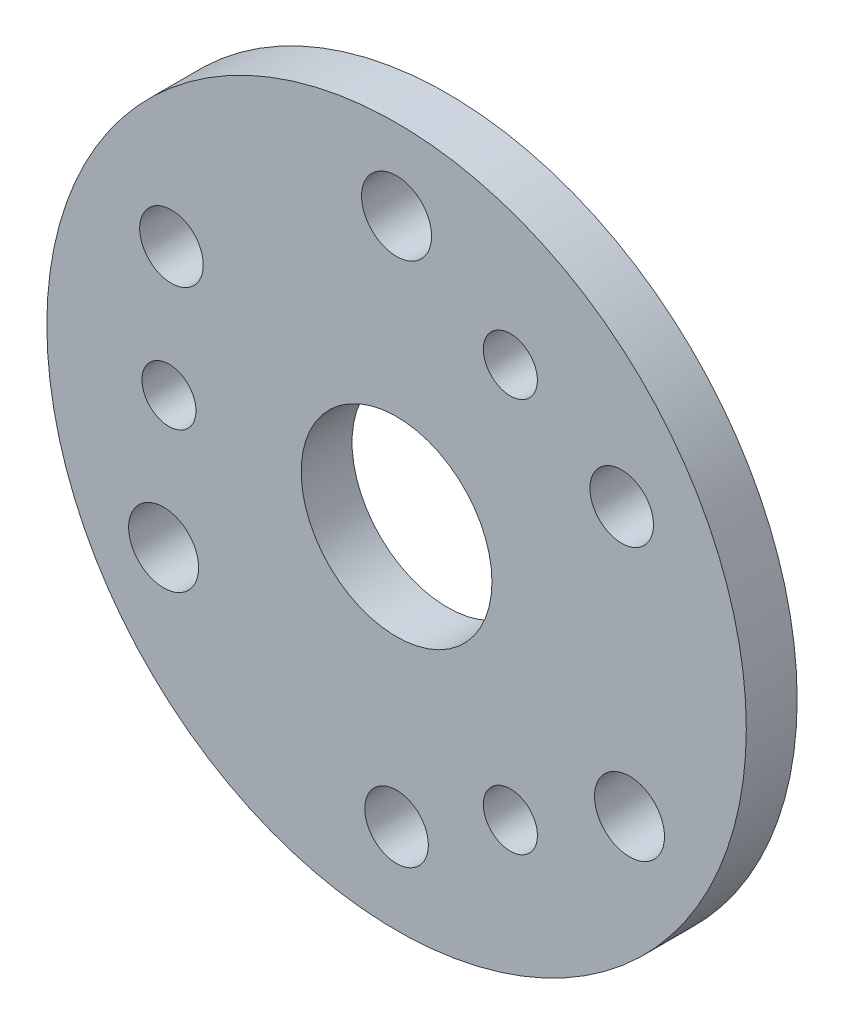
SolidWorks part; units mm, degrees
material "Acier S235"
ref_plane "Plan de face" through (0, 0, 0) normal (0, 0, 1) x (1, 0, 0)
ref_plane "Plan de dessus" through (0, 0, 0) normal (0, 1, 0) x (1, 0, 0)
ref_plane "Plan de droite" through (0, 0, 0) normal (1, 0, 0) x (0, 0, -1)
sketch "Esquisse1" plane through (0, 0, 0) normal (0, 0, 1) x (1, 0, 0)
  line L0 (0, 0) -> (17.8979, 31) construction
  line L1 (0, 0) -> (35.4, 20.4382) construction
  line L2 (0, 0) -> (0, 42.3) construction
  line L3 (35.4, 20.4382) -> (-35.4, 20.4382) construction
  line L4 (-35.4, 20.4382) -> (0, -40.8764) construction
  line L5 (0, -40.8764) -> (35.4, 20.4382) construction
  line L6 (17.8979, 31) -> (-35.7957, 0) construction
  line L7 (-35.7957, 0) -> (17.8979, -31) construction
  line L8 (17.8979, -31) -> (17.8979, 31) construction
  line L9 (-36.6329, -21.15) -> (0, 42.3) construction
  line L10 (0, 42.3) -> (36.6329, -21.15) construction
  line L11 (36.6329, -21.15) -> (-36.6329, -21.15) construction
  circle A0 centre (0, 0) radius 55
  circle A1 centre (0, 0) radius 15
  circle A2 centre (0, 0) radius 40.8764 construction
  circle A3 centre (0, 0) radius 35.7957 construction
  circle A4 centre (0, 0) radius 42.3 construction
  circle A5 centre (0, 42.3) radius 5.5
  circle A6 centre (17.8979, 31) radius 4.25
  circle A7 centre (35.4, 20.4382) radius 5
  circle A8 centre (36.6329, -21.15) radius 5.5
  circle A9 centre (17.8979, -31) radius 4.25
  circle A10 centre (0, -40.8764) radius 5
  circle A11 centre (-36.6329, -21.15) radius 5.5
  circle A12 centre (-35.7957, 0) radius 4.25
  circle A13 centre (-35.4, 20.4382) radius 5
  point P28 (0, 0)
  dimension "D1" = 30
  dimension "D2" = 110
  dimension "D3" = 84.6
  dimension "D4" = 71.5914
  dimension "D5" = 81.7528
  dimension "D6" = 11
  dimension "D10" = 8.5
  dimension "D11" = 10
  dimension "D12" = 70.8
  dimension "D7" = 30
  dimension "D8" = 60
  dimension "D13" = 62
  dimension "D14" = 73.2657
  dimension "D9" = 3
extrude "Boss.-Extru.1" add sketch "Esquisse1" along normal blind 8
